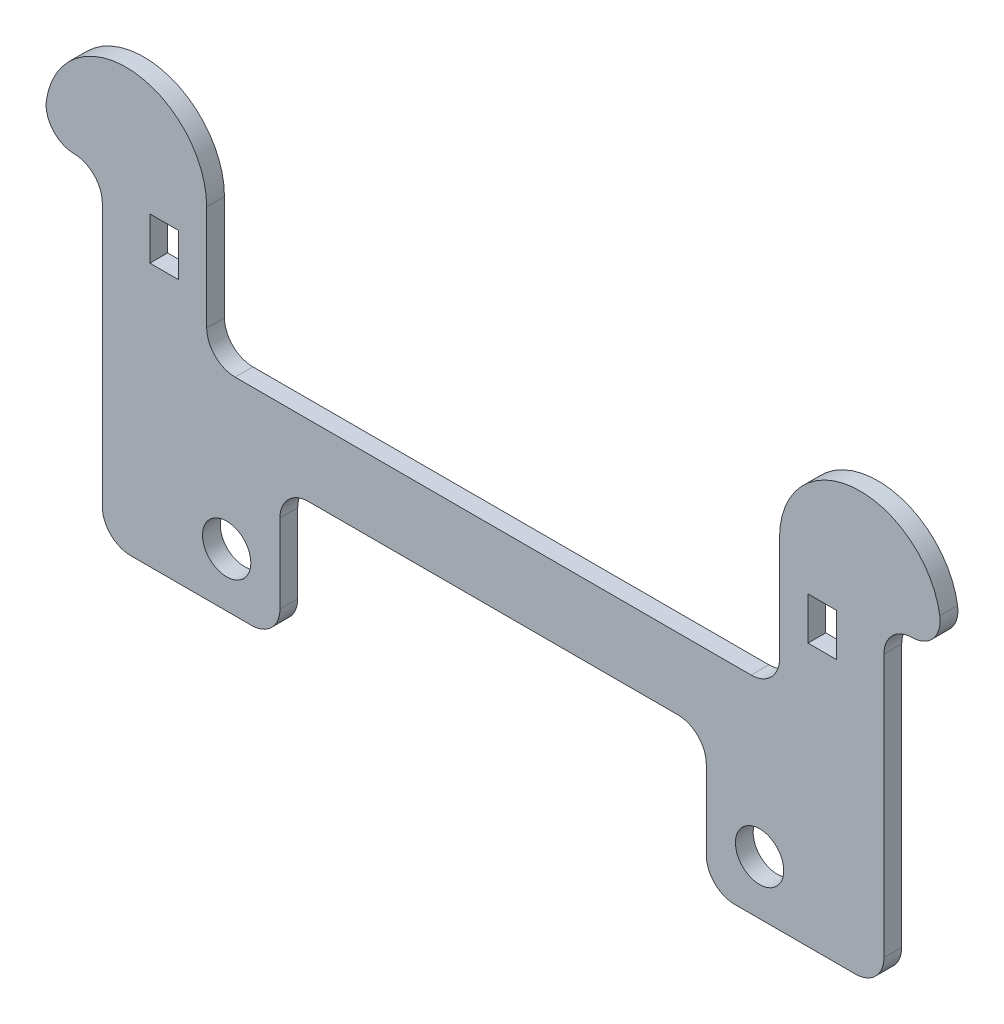
SolidWorks part; units mm, degrees
ref_plane "Front Plane" through (0, 0, 0) normal (0, 0, 1) x (1, 0, 0)
ref_plane "Top Plane" through (0, 0, 0) normal (0, 1, 0) x (1, 0, 0)
ref_plane "Right Plane" through (0, 0, 0) normal (1, 0, 0) x (0, 0, -1)
sketch "Sketch1" plane through (0, 0, 0) normal (0, 0, 1) x (1, 0, 0)
  line L0 (-5.08, 30.3964) -> (9.3289, 30.3964) construction
  line L5 (9.3289, 30.3964) -> (9.3289, 18.4831)
  line L7 (60.5211, 18.4831) -> (60.5211, 30.3964)
  line L8 (60.5211, 30.3964) -> (74.93, 30.3964) construction
  line L10 (11.1125, 4.8059) -> (58.7375, 4.8059) construction
  line L11 (15.875, 0) -> (15.875, 12.1331)
  line L12 (15.875, 12.1331) -> (53.975, 12.1331)
  line L13 (53.975, 12.1331) -> (53.975, 0)
  line L14 (53.975, 0) -> (69.85, 0)
  line L15 (15.875, 0) -> (0, 0)
  line L16 (0, 0) -> (0, 28.575)
  line L17 (0, 28.575) -> (-5.08, 28.575)
  line L18 (-5.08, 28.575) -> (-5.08, 30.3964)
  line L19 (34.925, 12.1331) -> (34.925, 4.8059) construction
  line L20 (69.85, 0) -> (69.85, 28.575)
  line L21 (69.85, 28.575) -> (74.93, 28.575)
  line L22 (74.93, 28.575) -> (74.93, 30.3964)
  line L23 (9.3289, 18.4831) -> (60.5211, 18.4831)
  circle A0 centre (11.1125, 4.8059) radius 2.159
  circle A1 centre (58.7375, 4.8059) radius 2.159
  arc A4 (-5.08, 30.3964) -> (9.3289, 30.3964) centre (2.1245, 30.3964) cw
  arc A5 (60.5211, 30.3964) -> (74.93, 30.3964) centre (67.7255, 30.3964) cw
  dimension "D1" = 4.318
  dimension "D5" = 7.3273
  dimension "D7" = 5.08
  dimension "D2" = 47.625
  dimension "D3" = 69.85
  dimension "D4" = 38.1
  dimension "D6" = 28.575
  dimension "D8" = 9.3289
  dimension "D10" = 1.8214
  dimension "D11" = 12.1331
  dimension "D12" = 11.9132
extrude "Boss-Extrude1" add sketch "Sketch1" along normal blind 1.5875
sketch "Sketch2" plane through (0, 0, 1.5875) normal (0, 0, 1) x (1, 0, 0)
  line L0 (6.7889, 25.4) -> (9.3289, 25.4) construction
  line L9 (4.2489, 27.305) -> (6.7889, 27.305)
  line L10 (4.2489, 27.305) -> (4.2489, 23.495)
  line L11 (4.2489, 23.495) -> (6.7889, 23.495)
  line L12 (6.7889, 27.305) -> (6.7889, 23.495)
  line L13 (63.0611, 27.305) -> (65.6011, 27.305)
  line L14 (63.0611, 27.305) -> (63.0611, 23.495)
  line L15 (63.0611, 23.495) -> (65.6011, 23.495)
  line L16 (65.6011, 27.305) -> (65.6011, 23.495)
  line L17 (60.5211, 25.4) -> (63.0611, 25.4) construction
  line L18 (9.3289, 18.4831) -> (9.3289, 30.3964) construction
  line L19 (60.5211, 30.3964) -> (60.5211, 18.4831) construction
  dimension "D1" = 2.54
  dimension "D3" = 2.54
  dimension "D7" = 3.81
extrude "Cut-Extrude1" cut sketch "Sketch2" against normal up to surface (1.5875 mm away) up to face at (13.2715, 4.8059, 0)
fillet "Fillet1" radius 2.54 10 edges at (15.875, 12.1331, 0.7937) (53.975, 12.1331, 0.7937) (53.975, 0, 0.7937) (15.875, 0, 0.7937) (0, 0, 0.7937) (69.85, 0, 0.7937) (69.85, 28.575, 0.7937) (0, 28.575, 0.7937) (60.5211, 18.4831, 0.7937) (9.3289, 18.4831, 0.7937)
fillet "Fillet2" radius 2.54 2 edges at (-5.08, 28.575, 0.7937) (74.93, 28.575, 0.7937)
